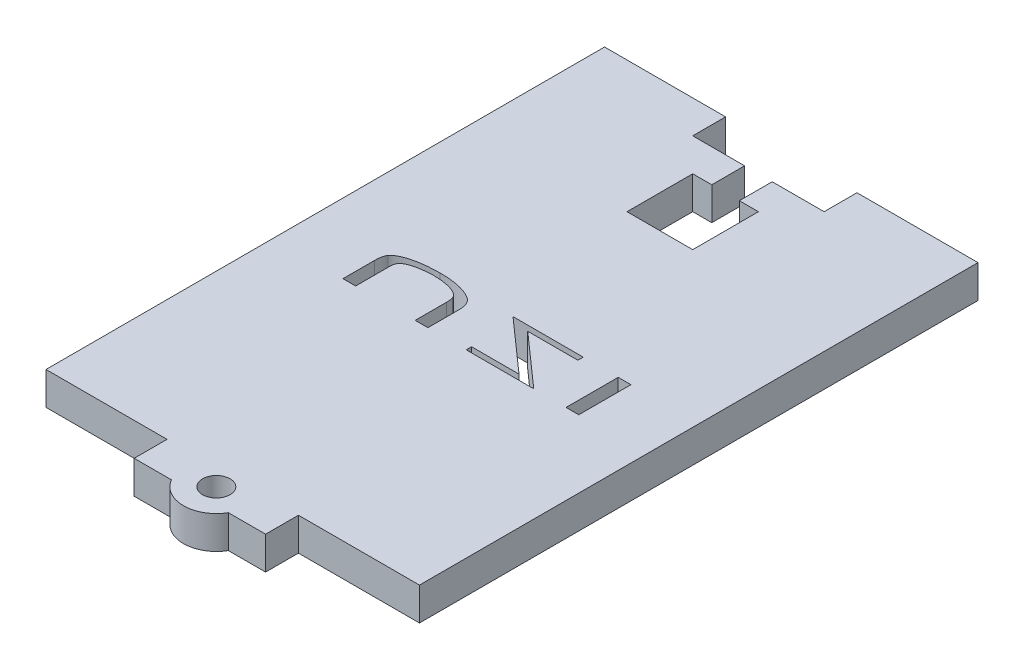
SolidWorks part; units mm, degrees
ref_plane "Front Plane" through (0, 0, 0) normal (0, 0, 1) x (1, 0, 0)
ref_plane "Top Plane" through (0, 0, 0) normal (0, 1, 0) x (1, 0, 0)
ref_plane "Right Plane" through (0, 0, 0) normal (1, 0, 0) x (0, 0, -1)
sketch "Sketch1" plane through (0, 0, 0) normal (0, 0, 1) x (1, 0, 0)
  line L1 (-134.1646, -69.4431) -> (-77.3309, -69.4431)
  line L2 (-134.1646, -69.4431) -> (-134.1646, -74.4431)
  line L3 (-134.1646, -74.4431) -> (-77.3309, -74.4431)
  line L4 (-77.3309, -69.4431) -> (-77.3309, -74.4431)
  dimension "D1" = 5
extrude "Boss-Extrude1" add sketch "Sketch1" along normal blind 80
sketch "Sketch2" plane through (0, 0, 0) normal (0, 0, -1) x (-1, 0, 0)
  line L0 (134.1646, -74.4431) -> (77.3309, -74.4431) construction
  line L1 (77.3309, -69.4431) -> (95.7478, -69.4431)
  line L2 (77.3309, -69.4431) -> (77.3309, -74.4431)
  line L3 (77.3309, -74.4431) -> (95.7478, -74.4431)
  line L4 (95.7478, -69.4431) -> (95.7478, -74.4431)
  line L5 (95.7478, -69.4431) -> (95.7478, -74.4431) construction
  line L6 (115.7478, -74.4431) -> (115.7478, -69.4431) construction
  line L7 (134.1646, -69.4431) -> (115.7478, -69.4431)
  line L8 (134.1646, -69.4431) -> (134.1646, -74.4431)
  line L9 (134.1646, -74.4431) -> (115.7478, -74.4431)
  line L10 (115.7478, -69.4431) -> (115.7478, -74.4431)
extrude "Boss-Extrude2" add sketch "Sketch2" along normal blind 5
sketch "Sketch3" plane through (0, 0, 80) normal (0, 0, 1) x (1, 0, 0)
  line L0 (-134.1646, -74.4431) -> (-77.3309, -74.4431) construction
  line L1 (-115.7478, -69.4431) -> (-95.7478, -69.4431)
  line L2 (-115.7478, -69.4431) -> (-115.7478, -74.4431)
  line L3 (-115.7478, -74.4431) -> (-95.7478, -74.4431)
  line L4 (-95.7478, -69.4431) -> (-95.7478, -74.4431)
  line L5 (-95.7478, -74.4431) -> (-95.7478, -69.4431) construction
extrude "Boss-Extrude3" add sketch "Sketch3" along normal blind 5
sketch "Sketch4" plane through (0, -74.4431, 0) normal (0, -1, 0) x (1, 0, 0)
  line L0 (-105.7478, 0) -> (-105.7478, 6.3937) construction
  line L1 (-115.7478, 0) -> (-95.7478, 0) construction
  line L2 (-107.8478, 0) -> (-107.8478, 5)
  line L3 (-107.8478, 5) -> (-110.7478, 5)
  line L4 (-110.7478, 5) -> (-110.7478, 15)
  line L5 (-110.7478, 15) -> (-100.7478, 15)
  line L6 (-100.7478, 15) -> (-100.7478, 5)
  line L7 (-100.7478, 5) -> (-103.6478, 5)
  line L8 (-103.6478, 5) -> (-103.6478, 0)
  line L9 (-107.8478, 0) -> (-103.6478, 0)
  dimension "D1" = 2.1
  dimension "D2" = 4.2
  dimension "D3" = 5
  dimension "D4" = 10
  dimension "D5" = 5
  dimension "D6" = 10
extrude "Cut-Extrude1" cut sketch "Sketch4" against normal blind 5
sketch "Sketch5" plane through (0, -74.4431, 0) normal (0, -1, 0) x (1, 0, 0)
  line L0 (-115.7478, 85) -> (-95.7478, 80) construction
  line L1 (-115.7478, 85) -> (-95.7478, 85) construction
  line L2 (-110.0779, 85) -> (-101.4176, 85)
  arc A0 (-101.4176, 85) -> (-110.0779, 85) centre (-105.7478, 82.5) ccw
  dimension "D1" = 10
extrude "Boss-Extrude4" add sketch "Sketch5" against normal blind 5
sketch "Sketch6" plane through (0, -74.4431, 0) normal (0, -1, 0) x (1, 0, 0)
  circle A0 centre (-105.7478, 82.5) radius 2.1
  dimension "D1" = 4.2
extrude "Cut-Extrude2" cut sketch "Sketch6" against normal blind 5
sketch "Sketch8" plane through (0, -74.4431, 0) normal (0, -1, 0) x (1, 0, 0)
  line L0 (-134.1646, 37.5) -> (-77.3309, 37.5) construction
  line L1 (-134.1646, 80) -> (-134.1646, -5) construction
  line L2 (-77.3309, 80) -> (-77.3309, -5) construction
  text T0 "UZI" font "Century Gothic" height in points 30
extrude "Cut-Extrude3" cut sketch "Sketch8" against normal blind 5
